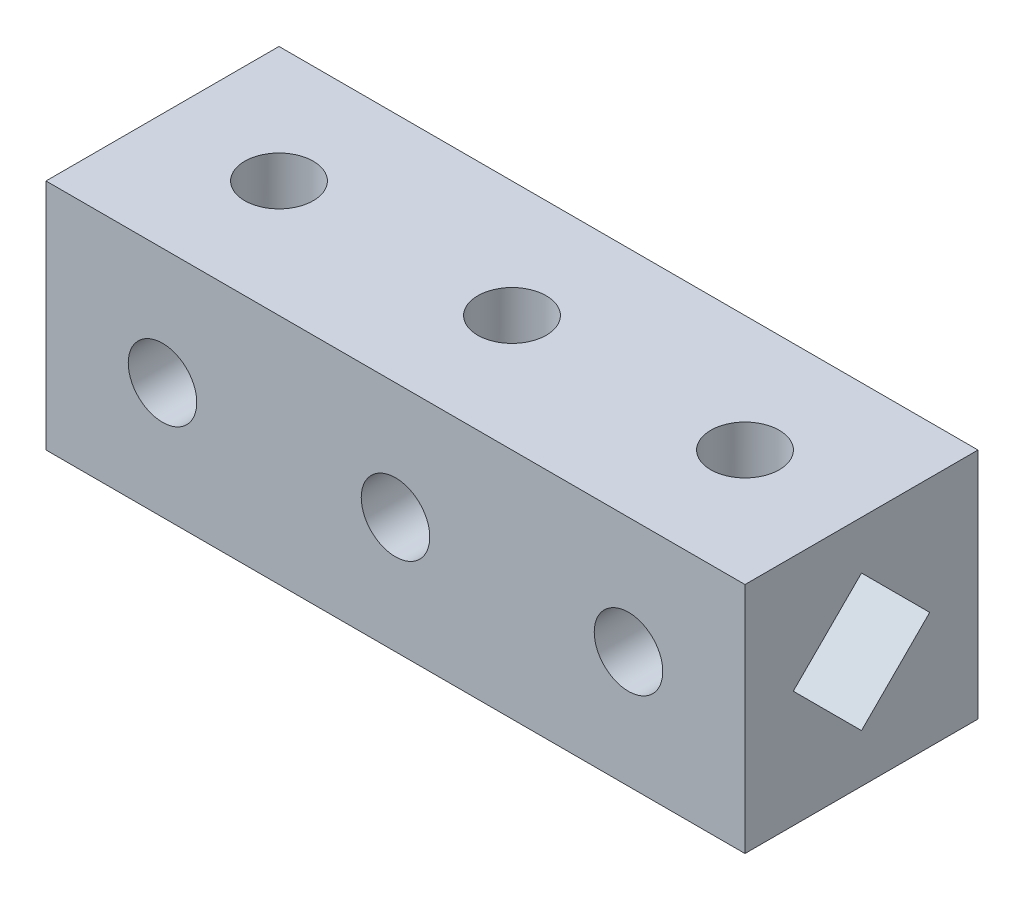
SolidWorks part; units mm, degrees
ref_plane "Front Plane" through (0, 0, 0) normal (0, 0, 1) x (1, 0, 0)
ref_plane "Top Plane" through (0, 0, 0) normal (0, 1, 0) x (1, 0, 0)
ref_plane "Right Plane" through (0, 0, 0) normal (1, 0, 0) x (0, 0, -1)
other "Configuration Table"
sketch "sketch1" plane through (0, 0, 0) normal (0, 1, 0) x (1, 0, 0)
  line L0 (0, -8.5) -> (8.5, -8.5) construction
  line L1 (0, 0) -> (51, 0)
  line L2 (0, 0) -> (0, -17)
  line L3 (0, -17) -> (51, -17)
  line L4 (51, 0) -> (51, -17)
  line L5 (8.5, -8.5) -> (25.5, -8.5) construction
  circle A1 centre (8.5, -8.5) radius 2.5
  circle A2 centre (25.5, -8.5) radius 2.5
  circle A3 centre (42.5, -8.5) radius 2.5
  dimension "D4" = 5
  dimension "D1" = 17
  dimension "D2" = 51
  dimension "D3" = 8.5
  dimension "D6" = 17
  dimension "D5" = 3
extrude "Boss-Extrude1" add sketch "sketch1" along normal blind 17
sketch "Sketch6" plane through (0, 0, 0) normal (0, 0, -1) x (-1, 0, 0)
  line L0 (-51, 8.5) -> (-42.5, 8.5) construction
  line L1 (-42.5, 8.5) -> (-25.5, 8.5) construction
  line L4 (-51, 0) -> (0, 0)
  line L5 (0, 0) -> (0, 17)
  line L6 (0, 17) -> (-51, 17)
  line L7 (-51, 17) -> (-51, 0)
  line L8 (-51, 0) -> (0, 0)
  line L9 (0, 0) -> (0, 17)
  line L10 (0, 17) -> (-51, 17)
  line L11 (-51, 17) -> (-51, 0)
  circle A0 centre (-42.5, 8.5) radius 2.5
  circle A1 centre (-25.5, 8.5) radius 2.5
  circle A2 centre (-8.5, 8.5) radius 2.5
  dimension "D3" = 5
  dimension "D2" = 8.5
  dimension "D5" = 17
  dimension "D1" = 0
  dimension "D4" = 3
extrude "Cut-Extrude10" cut sketch "Sketch6" against normal through all flip side to cut
sketch "Sketch7" plane through (51, 0, 0) normal (1, 0, 0) x (0, 0, -1)
  line L0 (-17, 8.5) -> (0, 8.5) construction
  line L1 (-8.5, 8.5) -> (-8.5, 13.478) construction
  line L2 (-8.5, 13.478) -> (-3.522, 8.5)
  line L3 (-3.522, 8.5) -> (-8.5, 3.522)
  line L4 (-17, 0) -> (0, 0)
  line L5 (0, 0) -> (0, 17)
  line L6 (0, 17) -> (-17, 17)
  line L7 (-17, 17) -> (-17, 0)
  line L8 (-17, 0) -> (0, 0)
  line L9 (0, 0) -> (0, 17)
  line L10 (0, 17) -> (-17, 17)
  line L11 (-17, 17) -> (-17, 0)
  line L12 (-8.5, 3.522) -> (-13.478, 8.5)
  line L13 (-13.478, 8.5) -> (-8.5, 13.478)
  dimension "D1" = 0
  dimension "D2" = 7.04
extrude "Cut-Extrude11" cut sketch "Sketch7" against normal blind 17 flip side to cut
sketch "Sketch9" plane through (0, 0, 0) normal (-1, 0, 0) x (0, 0, 1)
  line L4 (0, 0) -> (17, 0)
  line L5 (0, 17) -> (0, 0)
  line L6 (17, 17) -> (0, 17)
  line L7 (17, 0) -> (17, 17)
  line L8 (0, 0) -> (17, 0)
  line L9 (0, 17) -> (0, 0)
  line L10 (17, 17) -> (0, 17)
  line L11 (17, 0) -> (17, 17)
  line L12 (8.5, 13.478) -> (3.522, 8.5)
  line L13 (3.522, 8.5) -> (8.5, 3.522)
  line L14 (8.5, 3.522) -> (13.478, 8.5)
  line L15 (13.478, 8.5) -> (8.5, 13.478)
  line L16 (8.5, 13.478) -> (3.522, 8.5)
  line L17 (3.522, 8.5) -> (8.5, 3.522)
  line L18 (8.5, 3.522) -> (13.478, 8.5)
  line L19 (13.478, 8.5) -> (8.5, 13.478)
  dimension "D1" = 0
  dimension "D2" = 0
extrude "Cut-Extrude12" cut sketch "Sketch9" against normal blind 17 flip side to cut
equation "\"D2@sketch1\" = \"length\""
equation "\"holes\"= 3"
equation "\"cdist\"= 17mm'centre distance between holes"
equation "\"width\"= 17mm"
equation "\"length\"= \"cdist\" * \"holes\""
equation "\"D1@sketch1\" = \"width\""
equation "\"hdiam\"= 5mm'Hole diametre"
equation "\"D4@sketch1\" = \"hdiam\""
equation "\"D6@sketch1\" = \"cdist\""
equation "\"D5@sketch1\" = \"holes\""
equation "\"D2@Sketch6\"=\"cdist\"/2"
equation "\"D3@Sketch6\"=\"hdiam\""
equation "\"D5@Sketch6\"=\"cdist\""
equation "\"D4@Sketch6\"=\"holes\""
equation "\"D1@Boss-Extrude1\"=\"width\""
equation "\"insetwidth\"= 7mm"
equation "\"tolerance\"= 0.04mm"
equation "\"D2@Sketch7\"=\"insetwidth\"+\"tolerance\""
equation "\"D1@Cut-Extrude11\"=\"cdist\""
equation "\"D1@Cut-Extrude12\"=\"cdist\""
